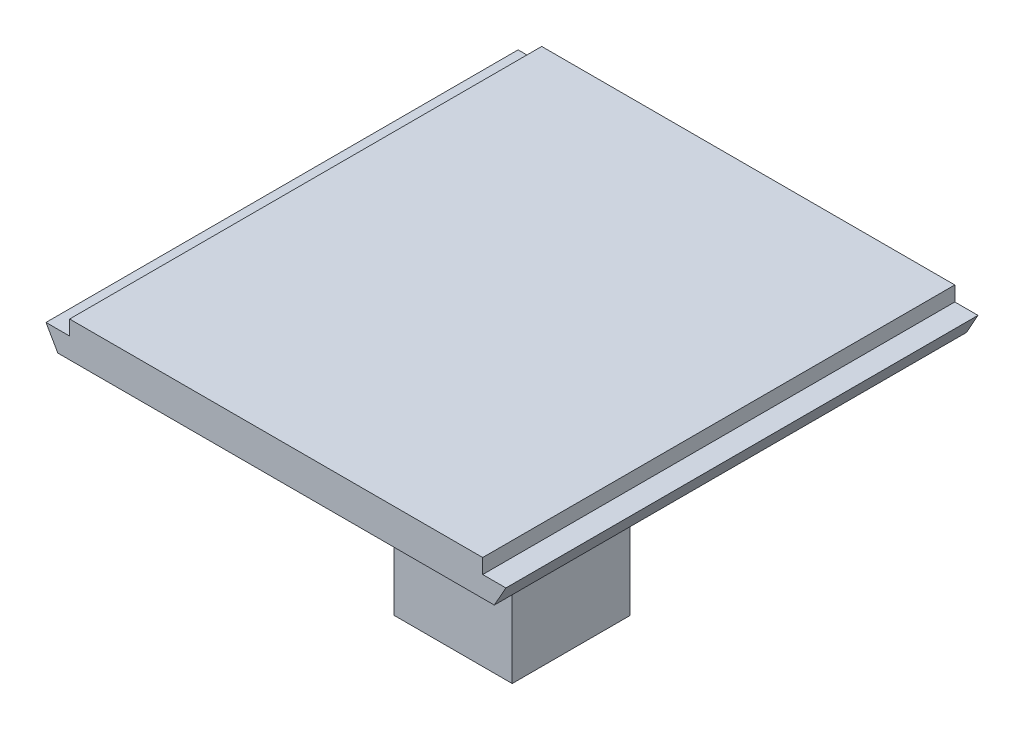
SolidWorks part; units mm, degrees
ref_plane "Front Plane" through (0, 0, 0) normal (0, 0, 1) x (1, 0, 0)
ref_plane "Top Plane" through (0, 0, 0) normal (0, 1, 0) x (1, 0, 0)
ref_plane "Right Plane" through (0, 0, 0) normal (1, 0, 0) x (0, 0, -1)
sketch "Sketch1" plane through (0, 0, 0) normal (0, 1, 0) x (1, 0, 0)
  line L1 (-69.85, 50.8) -> (69.85, 50.8)
  line L2 (-95.25, 25.4) -> (-95.25, -25.4)
  line L3 (-69.85, -50.8) -> (69.85, -50.8)
  line L4 (95.25, 25.4) -> (95.25, -25.4)
  line L5 (-95.25, 50.8) -> (95.25, -50.8) construction
  line L6 (-95.25, -50.8) -> (95.25, 50.8) construction
  arc A0 (69.85, 50.8) -> (95.25, 25.4) centre (69.85, 25.4) cw
  arc A1 (-95.25, -25.4) -> (-69.85, -50.8) centre (-69.85, -25.4) ccw
  arc A2 (-69.85, 50.8) -> (-95.25, 25.4) centre (-69.85, 25.4) ccw
  arc A3 (69.85, -50.8) -> (95.25, -25.4) centre (69.85, -25.4) ccw
  circle A4 centre (-69.85, 25.4) radius 6.35
  circle A6 centre (69.85, -25.4) radius 6.35
  circle A7 centre (69.85, 25.4) radius 6.35
  circle A9 centre (-69.85, -25.4) radius 6.35
  point P0 (0, 0)
  dimension "D3" = 25.4
  dimension "D4" = 12.7
  dimension "D5" = 12.7
  dimension "D6" = 12.7
  dimension "D7" = 12.7
  dimension "D1" = 101.6
  dimension "D2" = 190.5
extrude "Boss-Extrude2" add sketch "Sketch1" along normal blind 7.62 contours A3 L3 A1 L2 A2 L1 A0 L4 | A4 | A9 | A6 | A7
sketch "Sketch3" plane through (0, 7.62, 0) normal (0, 1, 0) x (1, 0, 0)
  line L0 (-44.45, 50.8) -> (-44.45, -50.8)
  line L1 (44.45, 50.8) -> (44.45, -50.8)
  line L4 (95.25, -25.4) -> (95.25, 25.4)
  line L5 (69.85, 50.8) -> (-69.85, 50.8)
  line L6 (-95.25, 25.4) -> (-95.25, -25.4)
  line L7 (-69.85, -50.8) -> (69.85, -50.8)
  line L8 (95.25, -25.4) -> (95.25, 25.4)
  line L9 (69.85, 50.8) -> (-69.85, 50.8)
  line L10 (-95.25, 25.4) -> (-95.25, -25.4)
  line L11 (-69.85, -50.8) -> (69.85, -50.8)
  arc A4 (95.25, 25.4) -> (69.85, 50.8) centre (69.85, 25.4) ccw
  arc A5 (-69.85, 50.8) -> (-95.25, 25.4) centre (-69.85, 25.4) ccw
  arc A6 (-95.25, -25.4) -> (-69.85, -50.8) centre (-69.85, -25.4) ccw
  arc A7 (69.85, -50.8) -> (95.25, -25.4) centre (69.85, -25.4) ccw
  arc A8 (95.25, 25.4) -> (69.85, 50.8) centre (69.85, 25.4) ccw
  arc A9 (-69.85, 50.8) -> (-95.25, 25.4) centre (-69.85, 25.4) ccw
  arc A10 (-95.25, -25.4) -> (-69.85, -50.8) centre (-69.85, -25.4) ccw
  arc A11 (69.85, -50.8) -> (95.25, -25.4) centre (69.85, -25.4) ccw
  circle M11 centre (69.85, -25.4) radius 6.35
  circle M12 centre (-69.85, 25.4) radius 6.35
  line M13 (95.25, -25.4) -> (95.25, 25.4)
  arc M14 (95.25, 25.4) -> (69.85, 50.8) centre (69.85, 25.4) ccw
  line M15 (69.85, 50.8) -> (-69.85, 50.8)
  arc M16 (-69.85, 50.8) -> (-95.25, 25.4) centre (-69.85, 25.4) ccw
  line M17 (-95.25, 25.4) -> (-95.25, -25.4)
  arc M18 (-95.25, -25.4) -> (-69.85, -50.8) centre (-69.85, -25.4) ccw
  line M19 (-69.85, -50.8) -> (69.85, -50.8)
  arc M20 (69.85, -50.8) -> (95.25, -25.4) centre (69.85, -25.4) ccw
  circle M21 centre (-69.85, -25.4) radius 6.35
  circle M22 centre (69.85, 25.4) radius 6.35
  dimension "D2" = 50.8
  dimension "D3" = 50.8
  dimension "D1" = 0
extrude "Cut-Extrude2" cut sketch "Sketch3" against normal blind 3.175 contours L0 M15 M16 M17 M18 M19 M12 M21 | L1 M15 M19 M20 M13 M14 M11 M22
sketch "Sketch4" plane through (0, 0, 0) normal (0, -1, 0) x (1, 0, 0)
  line L1 (-12.7, 12.7) -> (12.7, 12.7)
  line L2 (-12.7, 12.7) -> (-12.7, -12.7)
  line L3 (-12.7, -12.7) -> (12.7, -12.7)
  line L4 (12.7, 12.7) -> (12.7, -12.7)
  line L5 (-12.7, 12.7) -> (12.7, -12.7) construction
  line L6 (-12.7, -12.7) -> (12.7, 12.7) construction
  point P0 (0, 0)
  dimension "D1" = 25.4
  dimension "D2" = 25.4
extrude "Boss-Extrude3" add sketch "Sketch4" along normal blind 50.8 contours L2 L1 L4 L3
sketch "Sketch5" plane through (0, 0, 50.8) normal (0, 0, 1) x (1, 0, 0)
  line L0 (-49.53, 4.445) -> (-110.0265, 4.445)
  line L1 (-69.85, 4.445) -> (-44.45, 4.445) construction
  line L2 (-49.53, 4.445) -> (-46.99, 0)
  line L3 (-69.85, 0) -> (69.85, 0) construction
  line L4 (-110.0265, 4.445) -> (-110.0265, 0)
  line L5 (44.45, 4.445) -> (69.85, 4.445) construction
  line L6 (49.4409, 4.445) -> (46.9455, 0)
  line L7 (-110.0265, 0) -> (-46.99, 0)
  line L8 (49.4409, 4.445) -> (109.424, 4.445)
  line L9 (109.424, 4.445) -> (109.424, 0)
  line L10 (109.424, 0) -> (46.9455, 0)
extrude "Cut-Extrude4" cut sketch "Sketch5" against normal through all contours L7 L2 L0 L4 | L10 L6 L8 L9
